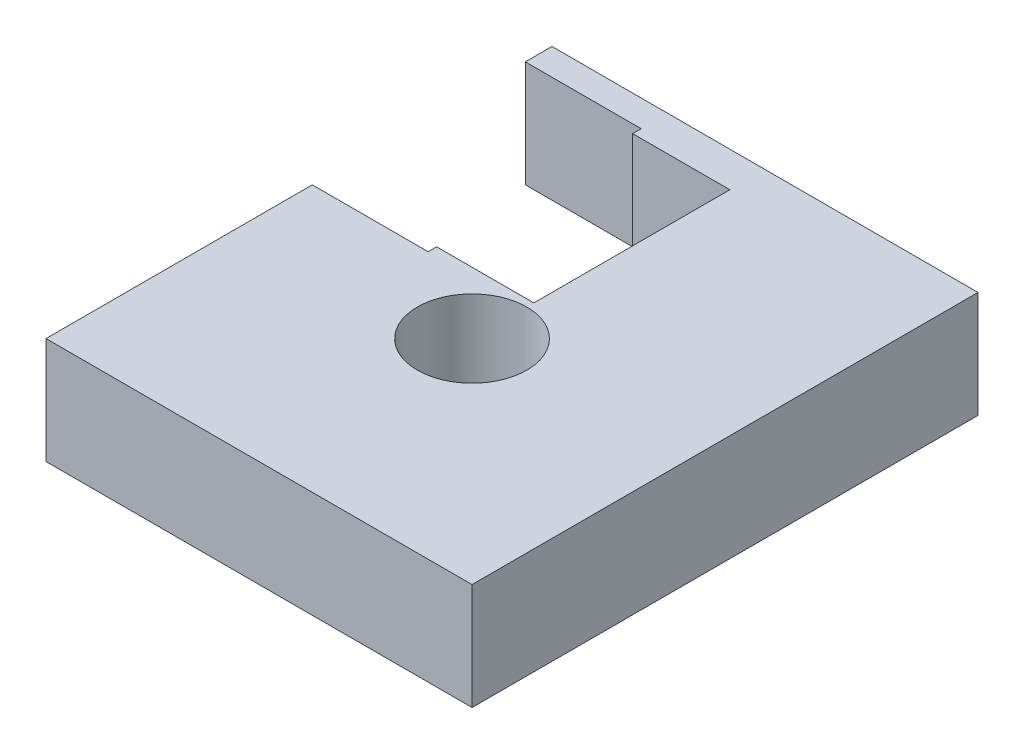
SolidWorks part; units mm, degrees
ref_plane "Front Plane" through (0, 0, 0) normal (0, 0, 1) x (1, 0, 0)
ref_plane "Top Plane" through (0, 0, 0) normal (0, 1, 0) x (1, 0, 0)
ref_plane "Right Plane" through (0, 0, 0) normal (1, 0, 0) x (0, 0, -1)
sketch "Sketch1" plane through (0, 0, 0) normal (0, 1, 0) x (1, 0, 0)
  line L0 (-12.7, 3.175) -> (12.7, 3.175) construction
  line L1 (-12.7, -3.175) -> (12.7, -3.175) construction
  line L2 (0, 3.175) -> (0, -3.175) construction
  line L4 (-12.7, -12.7) -> (12.7, -12.7)
  line L5 (-12.7, -12.7) -> (-12.7, 12.7)
  line L6 (-12.7, 12.7) -> (12.7, 12.7)
  line L7 (12.7, -12.7) -> (12.7, 12.7)
  line L8 (-12.7, -12.7) -> (12.7, 12.7) construction
  line L9 (-12.7, 12.7) -> (12.7, -12.7) construction
  line L10 (-12.7, 15.875) -> (-5.7912, 15.875)
  line L11 (-12.7, 15.875) -> (-12.7, 3.175)
  line L12 (-12.7, 3.175) -> (-5.7912, 3.175)
  line L13 (-5.7912, 15.875) -> (-5.7912, 3.175)
  line L14 (-12.7, 15.875) -> (-5.7912, 3.175) construction
  line L15 (-12.7, 3.175) -> (-5.7912, 15.875) construction
  line L16 (-5.7912, 15.0114) -> (-2.2225, 15.0114)
  line L17 (-5.7912, 15.0114) -> (-5.7912, 4.0386)
  line L18 (-5.7912, 4.0386) -> (-2.2225, 4.0386)
  line L19 (-2.2225, 15.0114) -> (-2.2225, 4.0386)
  circle A0 centre (0, 0) radius 3.175
  point P13 (-9.2456, 9.525)
  point P22 (-2.2225, 9.525)
  dimension "D1" = 6.35
  dimension "D2" = 25.4
  dimension "D3" = 25.4
  dimension "D4" = 12.7
  dimension "D5" = 6.9088
  dimension "D6" = 10.4775
  dimension "D7" = 10.9728
sketch "Sketch2" plane through (0, 0, 0) normal (0, 1, 0) x (1, 0, 0)
  line L0 (-12.7, 15.875) -> (-12.7, 17.4625)
  line L1 (-12.7, 17.4625) -> (12.7, 17.4625)
  line L2 (-12.7, 15.875) -> (-5.7912, 15.875)
  line L3 (-5.7912, 15.875) -> (-5.7912, 15.367)
  line L4 (-5.7912, 15.875) -> (-5.7912, 3.175) construction
  line L5 (-5.7912, 15.367) -> (0, 15.367)
  line L7 (12.7, 17.4625) -> (12.7, -12.7)
  line L8 (12.7, -12.7) -> (12.7, 12.7) construction
  line L9 (12.7, -12.7) -> (-12.7, -12.7)
  line L10 (-12.7, -12.7) -> (-12.7, 3.175)
  line L11 (-12.7, 3.175) -> (-5.7912, 3.175)
  line L12 (-5.7912, 3.175) -> (-5.7912, 3.683)
  line L13 (-5.7912, 3.683) -> (0, 3.683)
  line L14 (0, 3.683) -> (0, 15.367)
  point P3 (0, 0)
  dimension "D1" = 0.508
  dimension "D2" = 0.508
  dimension "D3" = 17.4625
extrude "Boss-Extrude1" add sketch "Sketch2" along normal blind 6.35
hole_wizard "1/4 Clearance Hole1" positions "Sketch4" profile "Sketch3" hole size "1/4" standard "ANSI Inch"
sketch "Sketch4" plane through (0, 6.35, 0) normal (0, 1, 0) x (1, 0, 0)
  point P0 (0, 0)
sketch "Sketch3" plane through (0, 6.35, 0) normal (1, 0, 0) x (0, 0, 1)
  line L0 (0, 0) -> (0, 8.3111)
  line L1 (0, 8.3111) -> (3.2639, 6.35)
  line L2 (3.2639, 6.35) -> (3.2639, 0)
  line L5 (3.2639, 0) -> (0, 0)
  line L10 (0, 8.3111) -> (-3.2639, 6.35) construction
  line L11 (0, -6.35) -> (0, 107.95) construction
  dimension "Hole Dia." = 6.5278
  dimension "Hole Depth" = 6.35
  dimension "Drill Angle" = 118
